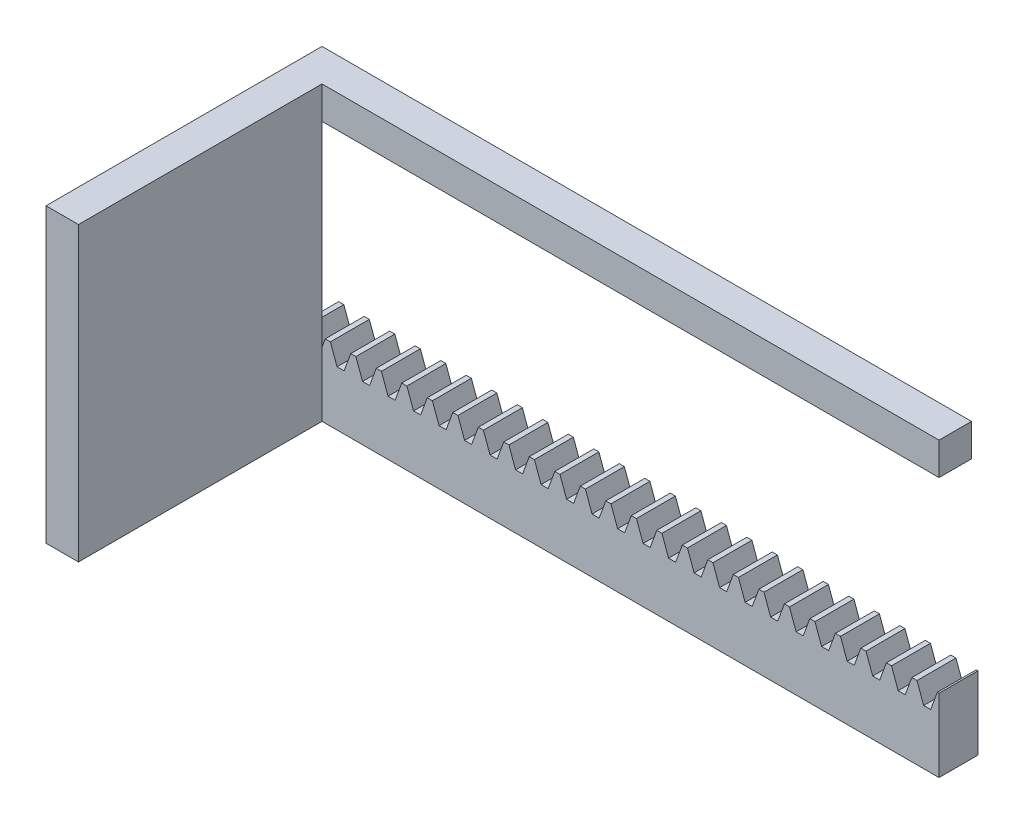
SolidWorks part; units mm, degrees
extrude "Blank" add sketch "BlankSke" against normal blind 12
sketch "BlankSke" plane through (0, 0, 0) normal (0, 0, 1) x (1, 0, 0)
  line L1 (0, 0) -> (200, 0)
  line L2 (0, 0) -> (0, 22.5)
  line L3 (0, 22.5) -> (200, 22.5)
  line L4 (200, 0) -> (200, 22.5)
  dimension "Length" = 200
  dimension "Blank_height" = 22.5
ref_plane "Plane1" through (0, 0, 0) normal (0, 0, 1) x (1, 0, 0)
ref_plane "Plane2" through (0, 0, 0) normal (0, 1, 0) x (1, 0, 0)
ref_plane "Plane3" through (0, 0, 0) normal (1, 0, 0) x (0, 0, -1)
sketch "HoldingSke" plane through (0, 0, 0) normal (0, 1, 0) x (1, 0, 0)
  line L0 (0, 0) -> (0.0557, 0.3961)
  line L1 (-15, 0) -> (100, 0) construction
  line L2 (0, 0) -> (-2.1039, 2.3779)
  line L3 (0, 0) -> (-11.863, 4.5341)
  line L4 (0, 0) -> (7.6947, 3.9206)
  line L5 (0, 0) -> (-23.7986, -8.8762)
  line L6 (0, 0) -> (-10.5278, -7.1032)
  line L9 (-71.009, 38.7566) -> (116.9296, 107.1606)
  line L10 (-76.2, 4.8779) -> (-56.2, 4.8779)
  line L11 (0, 0) -> (-12, 0)
  line L12 (-76.2, 101.6) -> (-76.113, 101.6)
  line L13 (24.9733, 27.94) -> (52.9518, 28.4284)
  line L14 (24.9733, 27.94) -> (24.9743, 27.94)
  line L15 (24.9733, 27.94) -> (100.4006, 29.5858)
  circle A0 centre (0, 0) radius 19.05
  circle A1 centre (0, 0) radius 10
  circle A2 centre (0, 0) radius 12.7
  dimension "MPH" = 20
  dimension "Diameter" = 38.1
  dimension "Num_teeth" = 27
  dimension "Pitch" = 0.4
  dimension "Show_teeth" = 998
  dimension "Thickness" = 12.7
  dimension "Ap" = 20
  dimension "Pitch_height" = 20
  dimension "Width" = 12
  dimension "Backlash" = 0.087
  dimension "Addendum_fac" = 1
  dimension "Dedendum_fac" = 1.25
  dimension "Clearance_fac" = 0.25
  dimension "Dedendum_add" = 0.001
  dimension "Length" = 200
  dimension "Module" = 2.5
sketch "TooCutSkeIll" plane through (0, 0, 0) normal (0, 0, 1) x (1, 0, 0)
  line L0 (-3.1105, 22.4342) -> (-1.237, 17.2869)
  line L1 (-0.6488, 16.875) -> (0.6488, 16.875)
  line L2 (1.237, 17.2869) -> (3.1105, 22.4342)
  line L3 (200, 22.5) -> (0, 22.5) construction
  line L4 (0, 0) -> (0, 64.897) construction
  line L5 (-13.208, 20) -> (12.954, 20) construction
  line L6 (0, 0) -> (200, 0) construction
  line L7 (2.2245, 20) -> (2.2245, 48.7463) construction
  line L8 (-2.2245, 20) -> (-2.2245, 48.7463) construction
  line L9 (3.2044, 22.5) -> (3.2044, 22.5254)
  line L10 (-3.2044, 22.5) -> (-3.2044, 22.5254)
  line L11 (-3.2044, 22.5254) -> (3.2044, 22.5254)
  arc A0 (0.6488, 16.875) -> (1.237, 17.2869) centre (0.6488, 17.501) ccw
  arc A1 (-1.237, 17.2869) -> (-0.6488, 16.875) centre (-0.6488, 17.501) ccw
  arc A2 (3.2044, 22.5) -> (3.1105, 22.4342) centre (3.2044, 22.4) ccw
  arc A3 (-3.1105, 22.4342) -> (-3.2044, 22.5) centre (-3.2044, 22.4) ccw
  dimension "Pitch_height" = 20
  dimension "Addendum_plus" = 2.5254
  dimension "Pressure_angle" = 20
  dimension "Gap_width" = 4.449
  dimension "Dedendum" = 3.125
extrude "ToothCutIll" [suppressed] cut sketch "TooCutSkeIll" against normal through all
sketch "TooCutSkeSim" plane through (0, 0, 0) normal (0, 0, 1) x (1, 0, 0)
  line L0 (1.0871, 16.875) -> (-1.0871, 16.875)
  line L1 (3.1437, 22.5254) -> (1.0871, 16.875)
  line L2 (0, 17.4625) -> (0, 53.467) construction
  line L3 (3.1437, 22.5254) -> (-3.1437, 22.5254)
  line L6 (-3.1437, 22.5254) -> (-1.0871, 16.875)
  line L9 (-2.2245, 20) -> (2.2245, 20) construction
  line L10 (0, 0) -> (200, 0) construction
  line L11 (2.2245, 20) -> (2.2245, 53.467) construction
  line L12 (-2.2245, 20) -> (-2.2245, 53.467) construction
  dimension "Pitch_height" = 20
  dimension "Addendum_plus" = 2.5254
  dimension "Pressure_angle" = 20
  dimension "Gap_width" = 4.449
  dimension "Dedendum" = 3.125
extrude "ToothCutSim" cut sketch "TooCutSkeSim" against normal through all
pattern_linear "TeethCuts" count 26 spacing 7.854 along (1, 0, 0) of "ToothCutIll", "ToothCutSim"
sketch "Sketch2" plane through (0, 0, 0) normal (0, 0, 1) x (1, 0, 0)
  line L0 (0, 0) -> (200, 0) construction
  line L1 (0, 0) -> (10, 0)
  line L2 (0, 0) -> (0, 90)
  line L3 (0, 90) -> (10, 90)
  line L4 (10, 0) -> (10, 90)
  line L5 (0, 16.875) -> (0, 0) construction
  dimension "D1" = 0
  dimension "D2" = 0
  dimension "D3" = 90
  dimension "D4" = 10
extrude "Boss-Extrude1" add sketch "Sketch2" along normal blind 75
sketch "Sketch3" plane through (0, 0, 0) normal (0, 0, -1) x (-1, 0, 0)
  line L0 (0, 90) -> (0, 16.875) construction
  line L1 (0, 90) -> (-200, 90)
  line L2 (0, 90) -> (0, 80)
  line L3 (0, 80) -> (-200, 80)
  line L4 (-200, 90) -> (-200, 80)
  line L5 (-10, 90) -> (0, 90) construction
  dimension "D1" = 10
  dimension "D2" = 200
  dimension "D3" = 0
  dimension "D4" = 0
extrude "Boss-Extrude2" add sketch "Sketch3" along normal blind 10
equation "' \"Module@HoldingSke\" = 6.35"
equation "' \"Num_teeth@HoldingSke\" = 12"
equation "' \"Ap@HoldingSke\" =  20"
equation "' \"Ap@HoldingSke\" = 20"
equation "' \"Width@HoldingSke\" = 0.25 * 25.4"
equation "' \"Show_teeth@HoldingSke\" = 500"
equation "' \"Backlash@HoldingSke\" = 0.009 * 25.4"
equation "' \"Addendum_fac@HoldingSke\" = 1.0"
equation "' \"Dedendum_fac@HoldingSke\" = 1.25"
equation "' \"Dedendum_add@HoldingSke\" = 0.00005 * 25.4"
equation "' \"Clearance_fac@HoldingSke\" = 0.25"
equation "' \"Pitch_height@HoldingSke\" = 1 * 25.4"
equation "' \"Length@HoldingSke\" = 4.71 * 25.4"
equation "\"Pitch@HoldingSke\" = 1 / \"Module@HoldingSke\""
equation "\"MPH@HoldingSke\" = \"Dedendum_fac@HoldingSke\" / \"Pitch@HoldingSke\" + 2 * \"Dedendum_add@HoldingSke\" + 0.002 * 25.4"
equation "\"MPH@HoldingSke\" = ((sgn( \"MPH@HoldingSke\" - \"Pitch_height@HoldingSke\")+1)*( \"MPH@HoldingSke\" - \"Pitch_height@HoldingSke\"))/2 + \"Pitch_height@HoldingSke\""
equation "\"Blank_height@BlankSke\" = \"Pitch_height@HoldingSke\" + \"Addendum_fac@HoldingSke\"  / \"Pitch@HoldingSke\" "
equation "\"Length@BlankSke\" =  \"Length@HoldingSke\""
equation "\"Face_width@Blank\" = \"Width@HoldingSke\""
equation "\"Pressure_angle@TooCutSkeIll\" = \"Ap@HoldingSke\""
equation "\"Addendum_plus@TooCutSkeIll\" =  \"Addendum_fac@HoldingSke\"  / \"Pitch@HoldingSke\" + 0.001 *25.4"
equation "\"Dedendum@TooCutSkeIll\" = \"Dedendum_fac@HoldingSke\"  / \"Pitch@HoldingSke\""
equation "\"Pitch_height@TooCutSkeIll\" =  \"MPH@HoldingSke\""
equation "\"Gap_width@TooCutSkeIll\" = 3.14159265 / 2 / \"Pitch@HoldingSke\" + 6 * \"Backlash@HoldingSke\""
equation "\"Pressure_angle@TooCutSkeSim\" = \"Ap@HoldingSke\""
equation "\"Addendum_plus@TooCutSkeSim\" =  \"Addendum_fac@HoldingSke\"  / \"Pitch@HoldingSke\" + 0.001 * 25.4"
equation "\"Dedendum@TooCutSkeSim\" = \"Dedendum_fac@HoldingSke\"  / \"Pitch@HoldingSke\""
equation "\"Pitch_height@TooCutSkeSim\" =  \"MPH@HoldingSke\""
equation "\"Gap_width@TooCutSkeSim\" = 3.14159265 / 2 / \"Pitch@HoldingSke\" + 6 * \"Backlash@HoldingSke\""
equation "\"Root_fillet@TooCutSkeIll\" = \"Clearance_fac@HoldingSke\" / \"Pitch@HoldingSke\" + \"Dedendum_add@HoldingSke\""
equation "\"Break_rad@TooCutSkeIll\" = 0.02 / \"Pitch@HoldingSke\" * 2"
equation "\"Linear_pitch@TeethCuts\" = 3.14159265 / \"Pitch@HoldingSke\""
equation "\"Num_teeth@HoldingSke\" = int( ( \"Length@HoldingSke\" + 0 ) / (3.14159265 / \"Pitch@HoldingSke\")) + 0.9999  + 1"
equation " \"Num_teeth@TeethCuts\" = int( \"Show_teeth@HoldingSke\" ) + 1"
equation " \"Num_teeth@TeethCuts\" = ((sgn( \"Num_teeth@TeethCuts\" - \"Num_teeth@HoldingSke\" )-1)*( \"Num_teeth@TeethCuts\" - \"Num_teeth@HoldingSke\" ))/-2+ \"Num_teeth@HoldingSke\""
equation " \"Num_teeth@TeethCuts\" = ((sgn( \"Num_teeth@TeethCuts\" - 2.0)+1)*( \"Num_teeth@TeethCuts\" - 2.0))/2 +2.0"
